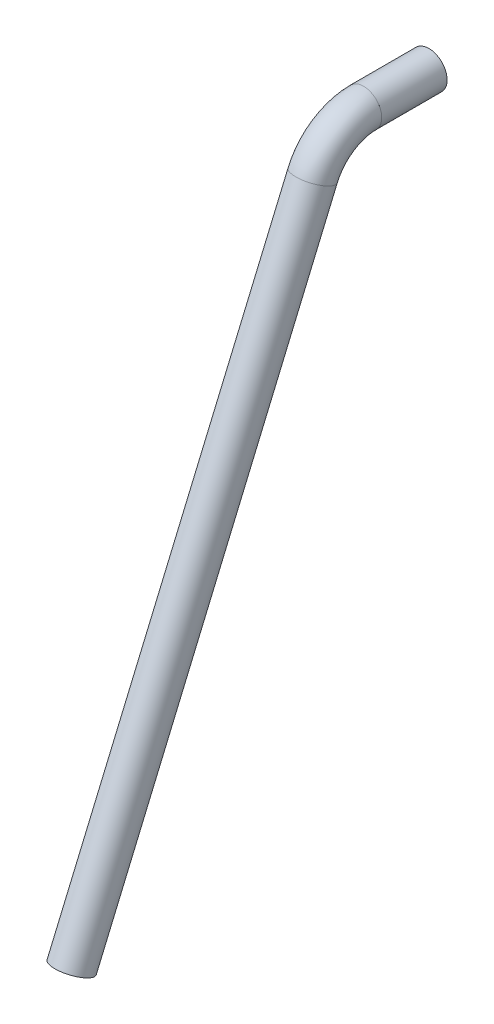
SolidWorks part; units mm, degrees
ref_plane "Alzado" through (0, 0, 0) normal (0, 0, 1) x (1, 0, 0)
ref_plane "Planta" through (0, 0, 0) normal (0, 1, 0) x (1, 0, 0)
ref_plane "Vista lateral" through (0, 0, 0) normal (1, 0, 0) x (0, 0, -1)
sketch "Croquis1" plane through (0, 0, 0) normal (1, 0, 0) x (0, 0, -1)
  line L0 (140.7348, 261.8252) -> (80.7348, 261.8252)
  line L1 (34.0038, 230.9462) -> (-187.1376, -287.8107)
  arc A0 (80.7348, 261.8252) -> (34.0038, 230.9462) centre (80.7348, 211.0252) ccw
other "Miembro estructural1"
ref_plane "Plano1" through (0, 230.9462, -34.0038) normal (0, -0.9199, 0.3921) x (0, -0.3921, -0.9199)
sketch "Sketch1" plane through (0, 230.9462, -34.0038) normal (0, -0.9199, 0.3921) x (0, -0.3921, -0.9199)
  circle A0 centre (0, 0) radius 13.3223
  circle A1 centre (0, 0) radius 16.7005
  circle A2 centre (0, 0) radius 12.7 construction
  point P5 (0, 0)
  dimension "In_dia" = 26.6446
  dimension "Out_dia" = 33.401
  dimension "D1" = 25.4
